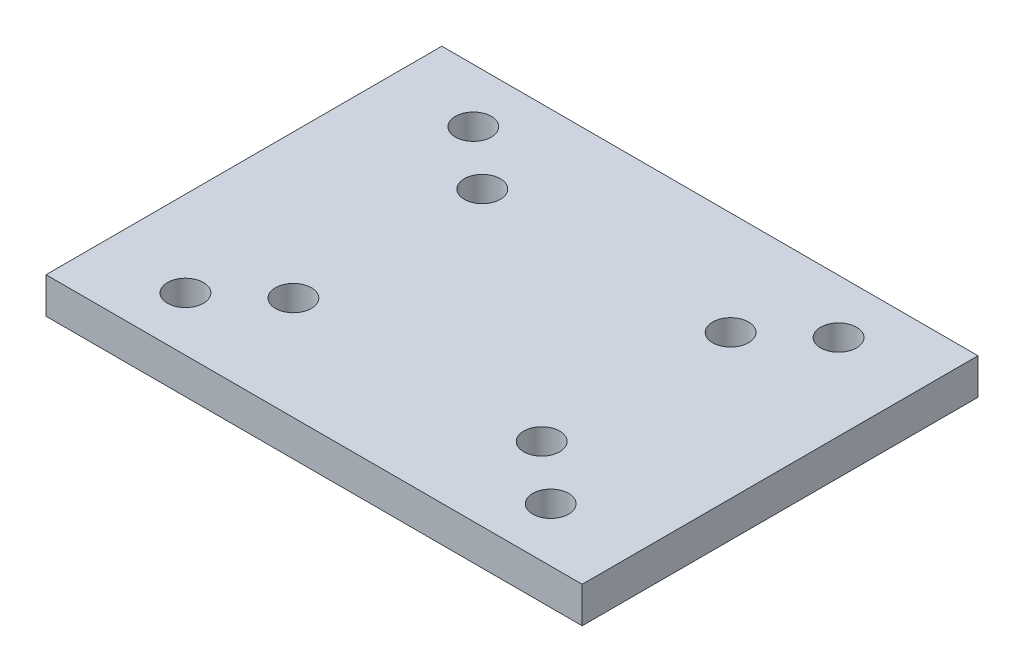
SolidWorks part; units mm, degrees
ref_plane "Front Plane" through (0, 0, 0) normal (0, 0, 1) x (1, 0, 0)
ref_plane "Top Plane" through (0, 0, 0) normal (0, 1, 0) x (1, 0, 0)
ref_plane "Right Plane" through (0, 0, 0) normal (1, 0, 0) x (0, 0, -1)
sketch "Sketch1" plane through (0, 0, 0) normal (0, 1, 0) x (1, 0, 0)
  line L1 (-14.9, -11) -> (14.9, -11)
  line L2 (-14.9, -11) -> (-14.9, 11)
  line L3 (-14.9, 11) -> (14.9, 11)
  line L4 (14.9, -11) -> (14.9, 11)
  line L5 (-14.9, -11) -> (14.9, 11) construction
  line L6 (-14.9, 11) -> (14.9, -11) construction
  circle A0 centre (10.15, 8) radius 1
  circle A1 centre (10.15, -8) radius 1
  circle A2 centre (-10.15, -8) radius 1
  circle A3 centre (-10.15, 8) radius 1
  point P0 (0, 0)
  dimension "D11" = 2
  dimension "D12" = 2
  dimension "D13" = 2
  dimension "D14" = 2
  dimension "D1" = 29.8
  dimension "D2" = 22
  dimension "D3" = 4.75
  dimension "D4" = 3
  dimension "D5" = 3
  dimension "D6" = 4.75
  dimension "D7" = 4.75
  dimension "D8" = 4.75
  dimension "D9" = 3
  dimension "D10" = 3
extrude "Boss-Extrude1" add sketch "Sketch1" along normal blind 2
sketch "Sketch2" plane through (0, 0, 0) normal (0, -1, 0) x (1, 0, 0)
  line L0 (14.9, -11) -> (-14.9, -11) construction
  line L1 (14.9, 11) -> (14.9, -11) construction
  line L2 (-14.9, -11) -> (-14.9, 11) construction
  circle A0 centre (6.9, -5.25) radius 1
  circle A1 centre (-6.9, -5.25) radius 1
  dimension "D5" = 2
  dimension "D6" = 2
  dimension "D1" = 5.75
  dimension "D2" = 5.75
  dimension "D3" = 8
  dimension "D4" = 8
extrude "Cut-Extrude1" cut sketch "Sketch2" against normal blind 10
ref_plane "Plane1" through (0, 0, 0) normal (0, 0, -1) x (-1, 0, 0)
mirror "Mirror1" about plane through (0, 0, 0) normal (0, 0, -1) of "Cut-Extrude1"
